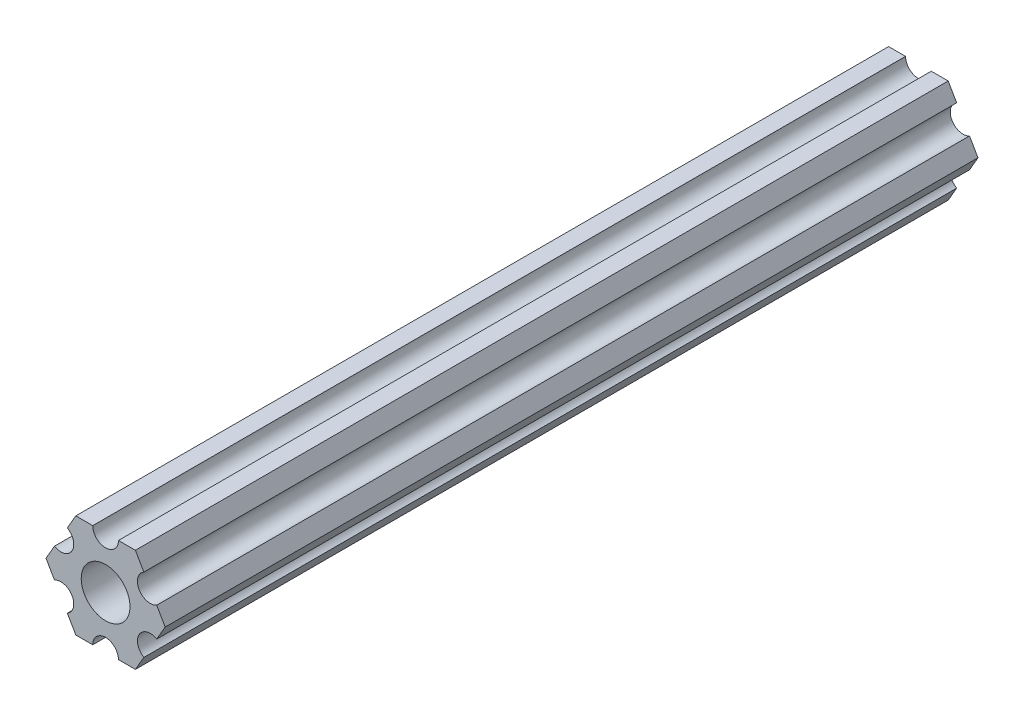
SolidWorks part; units mm, degrees
ref_plane "Ön Düzlem" through (0, 0, 0) normal (0, 0, 1) x (1, 0, 0)
ref_plane "Üst Düzlem" through (0, 0, 0) normal (0, 1, 0) x (1, 0, 0)
ref_plane "Sağ Düzlem" through (0, 0, 0) normal (1, 0, 0) x (0, 0, -1)
sketch "Çizim4" plane through (0, 0, 0) normal (0, 0, 1) x (1, 0, 0)
  line L0 (-3.6662, 6.35) -> (-1.5812, 6.35)
  line L1 (3.6662, 6.35) -> (4.7087, 4.5444)
  line L2 (7.3323, 0) -> (6.2899, -1.8056)
  line L3 (3.6662, -6.35) -> (1.5812, -6.35)
  line L4 (-3.6662, -6.35) -> (-4.7087, -4.5444)
  line L5 (-7.3323, 0) -> (-6.2899, 1.8056)
  line L6 (-4.7087, 4.5444) -> (-3.6662, 6.35)
  line L7 (1.5812, 6.35) -> (3.6662, 6.35)
  line L8 (6.2899, 1.8056) -> (7.3323, 0)
  line L9 (4.7087, -4.5444) -> (3.6662, -6.35)
  line L10 (-1.5812, -6.35) -> (-3.6662, -6.35)
  line L11 (-6.2899, -1.8056) -> (-7.3323, 0)
  circle A0 centre (0, 0) radius 2.9337
  arc A1 (1.5812, -6.35) -> (-1.5812, -6.35) centre (0, -6.35) ccw
  arc A2 (-4.7087, -4.5444) -> (-6.2899, -1.8056) centre (-5.4993, -3.175) ccw
  arc A3 (-6.2899, 1.8056) -> (-4.7087, 4.5444) centre (-5.4993, 3.175) ccw
  arc A4 (-1.5812, 6.35) -> (1.5812, 6.35) centre (0, 6.35) ccw
  arc A5 (4.7087, 4.5444) -> (6.2899, 1.8056) centre (5.4993, 3.175) ccw
  arc A6 (6.2899, -1.8056) -> (4.7087, -4.5444) centre (5.4993, -3.175) ccw
  point P18 (0, 0)
  dimension "D1" = 6
extrude "Yükseklik-Ekstrüzyon1" add sketch "Çizim4" along normal blind 100 contours A6 L9 L3 A1 L10 L4 A2 L11 L5 A3 L6 L0 A4 L7 L1 A5 L8 L2
sketch "Çizim6" plane through (0, 0, 0) normal (0, 0, -1) x (-1, 0, 0)
  circle A0 centre (0, 0) radius 3
  dimension "D1" = 6
extrude "Kes-Ekstrüzyon2" cut sketch "Çizim6" against normal through all both
